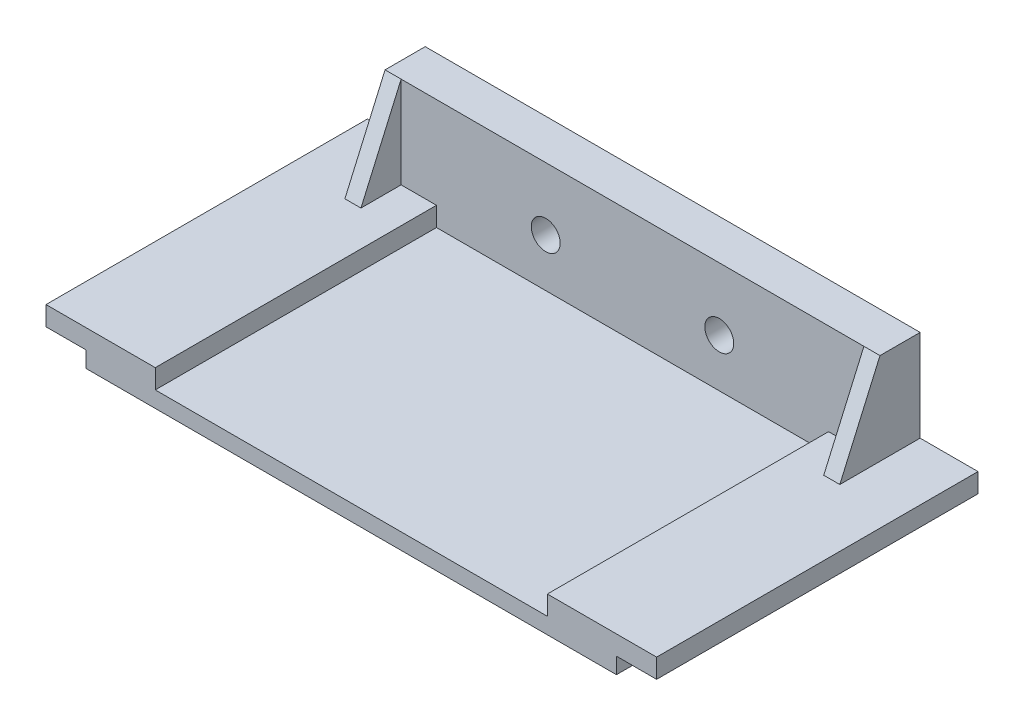
SolidWorks part; units mm, degrees
ref_plane "Front Plane" through (0, 0, 0) normal (0, 0, 1) x (1, 0, 0)
ref_plane "Top Plane" through (0, 0, 0) normal (0, 1, 0) x (1, 0, 0)
ref_plane "Right Plane" through (0, 0, 0) normal (1, 0, 0) x (0, 0, -1)
sketch "Sketch1" plane through (0, 0, 0) normal (0, 1, 0) x (1, 0, 0)
  line L1 (-48.26, -25.4) -> (48.26, -25.4)
  line L2 (-48.26, -25.4) -> (-48.26, 25.4)
  line L3 (-48.26, 25.4) -> (48.26, 25.4)
  line L4 (48.26, -25.4) -> (48.26, 25.4)
  line L5 (-48.26, -25.4) -> (48.26, 25.4) construction
  line L6 (-48.26, 25.4) -> (48.26, -25.4) construction
  point P0 (0, 0)
  dimension "D1" = 50.8
  dimension "D2" = 96.52
extrude "Boss-Extrude1" add sketch "Sketch1" along normal blind 5.588
sketch "Sketch2" plane through (0, 5.588, 0) normal (0, 1, 0) x (1, 0, 0)
  line L0 (48.26, 25.4) -> (-48.26, 25.4) construction
  line L1 (-30.988, -25.4) -> (30.988, -25.4)
  line L2 (-30.988, -25.4) -> (-30.988, 25.4)
  line L3 (-30.988, 25.4) -> (30.988, 25.4)
  line L4 (30.988, -25.4) -> (30.988, 25.4)
  line L5 (-30.988, -25.4) -> (30.988, 25.4) construction
  line L6 (-30.988, 25.4) -> (30.988, -25.4) construction
  point P0 (0, 0)
  line M6 (48.26, 25.4) -> (-48.26, 25.4)
  line M8 (-48.26, -25.4) -> (48.26, -25.4)
  dimension "D1" = 61.976
extrude "Cut-Extrude2" cut sketch "Sketch2" against normal blind 3.048 contours L4 L2 M8 M6
sketch "Sketch3" plane through (0, 0, 0) normal (0, -1, 0) x (-1, 0, 0)
  line L0 (48.26, -25.4) -> (-48.26, -25.4) construction
  line L1 (-48.26, 25.4) -> (-41.91, 25.4)
  line L2 (-48.26, 25.4) -> (-48.26, -25.4)
  line L3 (-48.26, -25.4) -> (-41.91, -25.4)
  line L4 (-41.91, 25.4) -> (-41.91, -25.4)
  line L6 (48.26, 25.4) -> (41.91, 25.4)
  line L7 (48.26, 25.4) -> (48.26, -25.4)
  line L8 (48.26, -25.4) -> (41.91, -25.4)
  line L9 (41.91, 25.4) -> (41.91, -25.4)
  dimension "D1" = 6.35
extrude "Cut-Extrude3" cut sketch "Sketch3" against normal blind 2.54
sketch "Sketch4" plane through (0, 2.54, 0) normal (0, 1, 0) x (1, 0, 0)
  line L0 (0, 0) -> (0, 50000) construction
  line L1 (30.988, 25.4) -> (-30.988, 25.4) construction
  line L2 (-39.116, 19.05) -> (39.116, 19.05)
  line L3 (-39.116, 19.05) -> (-39.116, 25.4)
  line L4 (-39.116, 25.4) -> (39.116, 25.4)
  line L5 (39.116, 19.05) -> (39.116, 25.4)
  line L6 (-39.116, 19.05) -> (39.116, 25.4) construction
  line L7 (-39.116, 25.4) -> (39.116, 19.05) construction
  point P3 (0, 22.225)
  dimension "D1" = 78.232
  dimension "D2" = 6.35
extrude "Boss-Extrude2" add sketch "Sketch4" along normal blind 17.526
sketch "Sketch5" plane through (0, 0, -25.4) normal (0, 0, -1) x (-1, 0, 0)
  line L0 (13.716, 10.16) -> (-13.716, 10.16) construction
  line L1 (39.116, 20.066) -> (39.116, 5.588) construction
  line L2 (-39.116, 20.066) -> (-39.116, 5.588) construction
  line L3 (-39.116, 20.066) -> (39.116, 20.066) construction
  circle A0 centre (13.716, 10.16) radius 2.286
  circle A1 centre (-13.716, 10.16) radius 2.286
  dimension "D1" = 4.572
  dimension "D2" = 25.4
  dimension "D3" = 25.4
  dimension "D4" = 9.906
extrude "Cut-Extrude4" cut sketch "Sketch5" against normal through all
sketch "Sketch6" plane through (-39.116, 0, 0) normal (-1, 0, 0) x (0, 0, 1)
  line L0 (-19.05, 5.588) -> (-12.7, 5.588)
  line L1 (-12.7, 5.588) -> (-19.05, 20.066)
  line L6 (-25.4, 20.066) -> (-25.4, 5.588)
  line L7 (-25.4, 5.588) -> (-19.05, 5.588)
  line L8 (-19.05, 5.588) -> (-19.05, 20.066)
  line L9 (-19.05, 20.066) -> (-25.4, 20.066)
  line L12 (-19.05, 5.588) -> (-19.05, 20.066)
  dimension "D1" = 6.35
  dimension "D2" = 0
extrude "Boss-Extrude3" add sketch "Sketch6" against normal blind 2.54
sketch "Sketch7" plane through (39.116, 0, 0) normal (1, 0, 0) x (0, 0, -1)
  line L3 (19.05, 5.588) -> (19.05, 20.066)
  line L4 (19.05, 20.066) -> (12.7, 5.588)
  line L5 (12.7, 5.588) -> (19.05, 5.588)
  line L6 (19.05, 5.588) -> (19.05, 20.066)
  line L7 (19.05, 20.066) -> (12.7, 5.588)
  line L8 (12.7, 5.588) -> (19.05, 5.588)
  dimension "D1" = 0
extrude "Boss-Extrude4" add sketch "Sketch7" against normal blind 2.54
sketch "Sketch8" plane through (0, 5.588, 0) normal (0, 1, 0) x (1, 0, 0)
  line L1 (48.26, 25.4) -> (41.91, 25.4)
  line L2 (48.26, 25.4) -> (48.26, 16.51)
  line L3 (48.26, 16.51) -> (41.91, 16.51)
  line L4 (41.91, 25.4) -> (41.91, 16.51)
  line L5 (-48.26, 25.4) -> (-41.91, 25.4)
  line L6 (-48.26, 25.4) -> (-48.26, 16.51)
  line L7 (-48.26, 16.51) -> (-41.91, 16.51)
  line L8 (-41.91, 25.4) -> (-41.91, 16.51)
  line L10 (-36.576, 19.05) -> (-30.988, 19.05) construction
  dimension "D1" = 2.54
extrude "Cut-Extrude5" cut sketch "Sketch8" against normal through all
sketch "Sketch9" plane through (0, 0, -16.51) normal (0, 0, -1) x (-1, 0, 0)
  line L0 (-48.26, 2.54) -> (-41.91, 2.54) construction
  line L1 (-41.91, 2.54) -> (-41.91, 5.588) construction
  line L2 (-41.91, 5.588) -> (-48.26, 5.588) construction
  line L3 (-48.26, 5.588) -> (-48.26, 2.54) construction
  line L4 (48.26, 2.54) -> (48.26, 5.588) construction
  line L5 (48.26, 5.588) -> (41.91, 5.588) construction
  line L6 (41.91, 5.588) -> (41.91, 2.54) construction
  line L7 (41.91, 2.54) -> (48.26, 2.54) construction
  line L8 (-48.26, 2.54) -> (-41.91, 2.54)
  line L9 (-41.91, 2.54) -> (-41.91, 5.588)
  line L10 (-41.91, 5.588) -> (-48.26, 5.588)
  line L11 (-48.26, 5.588) -> (-48.26, 2.54)
  line L12 (48.26, 2.54) -> (48.26, 5.588)
  line L13 (48.26, 5.588) -> (41.91, 5.588)
  line L14 (41.91, 5.588) -> (41.91, 2.54)
  line L15 (41.91, 2.54) -> (48.26, 2.54)
extrude "Boss-Extrude5" add sketch "Sketch9" along normal up to surface (8.89 mm away)
